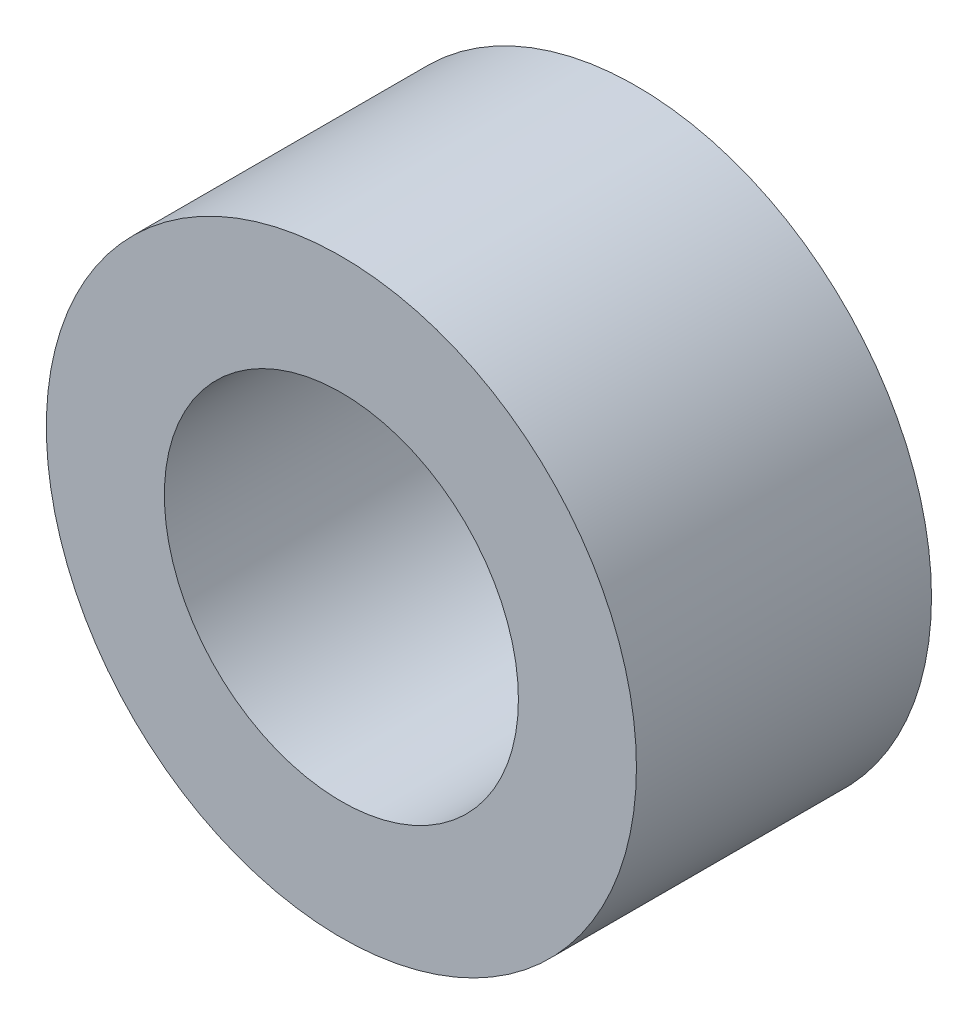
SolidWorks part; units mm, degrees
ref_plane "前视基准面" through (0, 0, 0) normal (0, 0, 1) x (1, 0, 0)
ref_plane "上视基准面" through (0, 0, 0) normal (0, 1, 0) x (1, 0, 0)
ref_plane "右视基准面" through (0, 0, 0) normal (1, 0, 0) x (0, 0, -1)
sketch "草图1" plane through (0, 0, 0) normal (0, 0, 1) x (1, 0, 0)
  circle A0 centre (0, 0) radius 1.5
  circle A1 centre (0, 0) radius 2.5
  dimension "D1" = 5
  dimension "D2" = 3
extrude "凸台-拉伸1" add sketch "草图1" along normal blind 2.5
